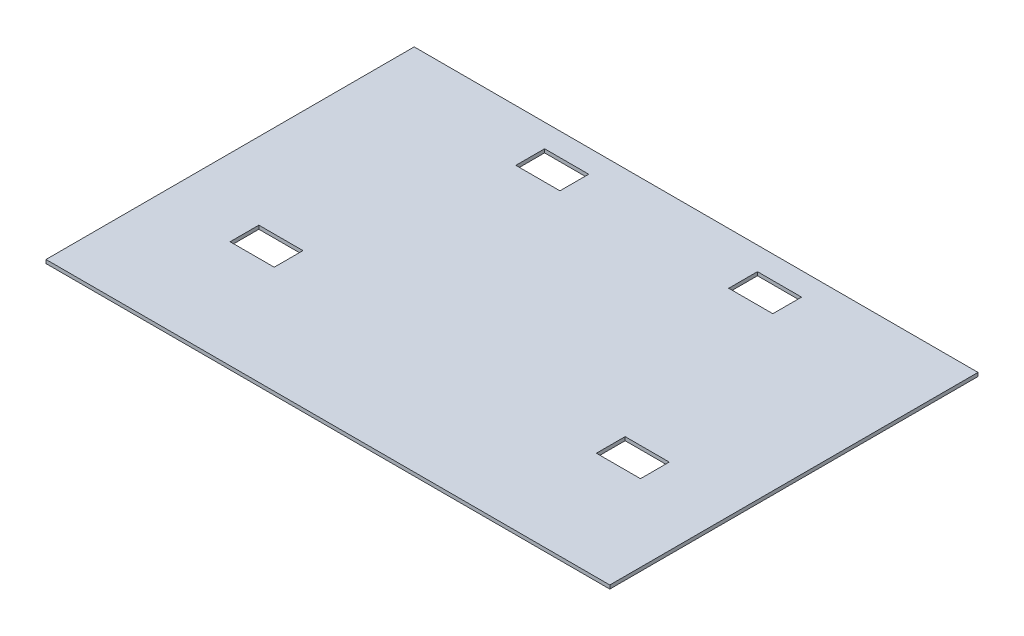
SolidWorks part; units mm, degrees
material "Pine"
ref_plane "Front Plane" through (0, 0, 0) normal (0, 0, 1) x (1, 0, 0)
ref_plane "Top Plane" through (0, 0, 0) normal (0, 1, 0) x (1, 0, 0)
ref_plane "Right Plane" through (0, 0, 0) normal (1, 0, 0) x (0, 0, -1)
other "Configuration Table"
sketch "Sketch1" plane through (0, 0, 0) normal (0, 1, 0) x (1, 0, 0)
  line L1 (-933.45, -609.6) -> (933.45, -609.6)
  line L2 (-933.45, -609.6) -> (-933.45, 609.6)
  line L3 (-933.45, 609.6) -> (933.45, 609.6)
  line L4 (933.45, -609.6) -> (933.45, 609.6)
  line L5 (-933.45, -609.6) -> (933.45, 609.6) construction
  line L6 (-933.45, 609.6) -> (933.45, -609.6) construction
  point P0 (0, 0)
  dimension "D1" = 1866.9
  dimension "D2" = 1219.2
extrude "Boss-Extrude1" add sketch "Sketch1" along normal mid plane 11.9062
sketch "Sketch2" [suppressed] plane through (0, 6.35, 0) normal (0, 1, 0) x (1, 0, 0)
  line L0 (1219.2, 609.6) -> (-1219.2, 609.6) construction
  line L1 (-1219.2, -609.6) -> (406.4, -609.6)
  line L2 (-1219.2, -609.6) -> (-1219.2, 254)
  line L3 (-1219.2, 254) -> (406.4, 254)
  line L4 (406.4, -609.6) -> (406.4, 254)
  line L5 (1219.2, -609.6) -> (1219.2, 609.6) construction
  dimension "D1" = 355.6
  dimension "D2" = 812.8
extrude "Cut-Extrude1" [suppressed] cut sketch "Sketch2" against normal through all
sketch "Sketch3" [suppressed] plane through (0, -5.9531, 0) normal (0, -1, 0) x (1, 0, 0)
  line L0 (58.7375, -28.575) -> (-58.7375, -28.575) construction
  line L1 (385.7625, -304.8) -> (-385.7625, -304.8) construction
  line L2 (-14.2875, 19.05) -> (131.7625, 19.05)
  line L3 (-14.2875, 19.05) -> (-14.2875, -76.2)
  line L4 (-14.2875, -76.2) -> (131.7625, -76.2)
  line L5 (131.7625, 19.05) -> (131.7625, -76.2)
  line L6 (-14.2875, 19.05) -> (131.7625, -76.2) construction
  line L7 (-14.2875, -76.2) -> (131.7625, 19.05) construction
  line L8 (-131.7625, 19.05) -> (14.2875, 19.05)
  line L9 (-131.7625, 19.05) -> (-131.7625, -76.2)
  line L10 (-131.7625, -76.2) -> (14.2875, -76.2)
  line L11 (14.2875, 19.05) -> (14.2875, -76.2)
  line L12 (-131.7625, 19.05) -> (14.2875, -76.2) construction
  line L13 (-131.7625, -76.2) -> (14.2875, 19.05) construction
  line L14 (385.7625, 304.8) -> (385.7625, -304.8) construction
  point P4 (0, -28.575)
  dimension "D1" = 146.05
  dimension "D2" = 95.25
  dimension "D3" = 254
  dimension "D4" = 228.6
extrude "Cut-Extrude2" [suppressed] cut sketch "Sketch3" against normal through all
sketch "Sketch12" [suppressed] plane through (0, 6.35, 0) normal (0, 1, 0) x (1, 0, 0)
  line L0 (-127, -317.5) -> (685.8, -317.5) construction
  line L1 (542.925, -220.6625) -> (446.0875, -220.6625)
  line L2 (542.925, -220.6625) -> (542.925, -317.5)
  line L3 (542.925, -317.5) -> (446.0875, -317.5)
  line L4 (446.0875, -220.6625) -> (446.0875, -317.5)
  line L5 (685.8, -317.5) -> (685.8, 317.5) construction
  line L6 (-127, -317.5) -> (-127, -38.1) construction
  line L7 (38.1, -220.6625) -> (134.9375, -220.6625)
  line L8 (38.1, -220.6625) -> (38.1, -317.5)
  line L9 (38.1, -317.5) -> (134.9375, -317.5)
  line L10 (134.9375, -220.6625) -> (134.9375, -317.5)
  dimension "D1" = 96.8375
  dimension "D2" = 142.875
  dimension "D3" = 165.1
extrude "Cut-Extrude10" [suppressed] cut sketch "Sketch12" against normal through all
sketch "Sketch11" [suppressed] plane through (0, -5.9531, 0) normal (0, -1, 0) x (1, 0, 0)
  line L0 (385.7625, 304.8) -> (385.7625, -304.8) construction
  line L1 (334.9625, 65.0875) -> (385.7625, 65.0875)
  line L2 (334.9625, 65.0875) -> (334.9625, 161.925)
  line L3 (334.9625, 161.925) -> (385.7625, 161.925)
  line L4 (385.7625, 65.0875) -> (385.7625, 161.925)
  line L5 (385.7625, -304.8) -> (-385.7625, -304.8) construction
  line L6 (-385.7625, 304.8) -> (385.7625, 304.8) construction
  line L7 (334.9625, -47.625) -> (385.7625, -47.625)
  line L8 (334.9625, -47.625) -> (334.9625, -144.4625)
  line L9 (334.9625, -144.4625) -> (385.7625, -144.4625)
  line L10 (385.7625, -47.625) -> (385.7625, -144.4625)
  dimension "D1" = 50.8
  dimension "D2" = 96.8375
  dimension "D3" = 142.875
  dimension "D4" = 160.3375
extrude "Cut-Extrude9" [suppressed] cut sketch "Sketch11" against normal through all
sketch "Sketch4" plane through (0, -5.9531, 0) normal (0, -1, 0) x (1, 0, 0)
  line L0 (0, 206.375) -> (0, -485.775) construction
  line L1 (606.425, 206.375) -> (-606.425, 206.375) construction
  line L2 (352.425, -485.775) -> (-352.425, -485.775) construction
  line L3 (933.45, 609.6) -> (933.45, -609.6) construction
  line L4 (425.45, -533.4) -> (279.4, -533.4)
  line L5 (425.45, -533.4) -> (425.45, -438.15)
  line L6 (425.45, -438.15) -> (279.4, -438.15)
  line L7 (279.4, -533.4) -> (279.4, -438.15)
  line L8 (425.45, -533.4) -> (279.4, -438.15) construction
  line L9 (425.45, -438.15) -> (279.4, -533.4) construction
  line L10 (-279.4, -533.4) -> (-425.45, -533.4)
  line L11 (-279.4, -533.4) -> (-279.4, -438.15)
  line L12 (-279.4, -438.15) -> (-425.45, -438.15)
  line L13 (-425.45, -533.4) -> (-425.45, -438.15)
  line L14 (-279.4, -533.4) -> (-425.45, -438.15) construction
  line L15 (-279.4, -438.15) -> (-425.45, -533.4) construction
  line L16 (-533.4, 158.75) -> (-679.45, 158.75)
  line L17 (-533.4, 158.75) -> (-533.4, 254)
  line L18 (-533.4, 254) -> (-679.45, 254)
  line L19 (-679.45, 158.75) -> (-679.45, 254)
  line L20 (-533.4, 158.75) -> (-679.45, 254) construction
  line L21 (-533.4, 254) -> (-679.45, 158.75) construction
  line L22 (679.45, 158.75) -> (533.4, 158.75)
  line L23 (679.45, 158.75) -> (679.45, 254)
  line L24 (679.45, 254) -> (533.4, 254)
  line L25 (533.4, 158.75) -> (533.4, 254)
  line L26 (679.45, 158.75) -> (533.4, 254) construction
  line L27 (679.45, 254) -> (533.4, 158.75) construction
  line L29 (-933.45, 609.6) -> (933.45, 609.6) construction
  line L30 (933.45, -609.6) -> (-933.45, -609.6) construction
  point P8 (0, 206.375)
  point P11 (0, -485.775)
  dimension "D1" = 146.05
  dimension "D2" = 95.25
  dimension "D3" = 254
  dimension "D4" = 76.2
  dimension "D5" = 355.6
  dimension "D6" = 508
extrude "Cut-Extrude3" cut sketch "Sketch4" against normal through all
sketch "Sketch5" [suppressed] plane through (0, 6.35, 0) normal (0, 1, 0) x (1, 0, 0)
  line L0 (-127, -38.1) -> (-685.8, -38.1) construction
  line L1 (685.8, 317.5) -> (-685.8, 317.5) construction
  line L3 (685.8, -317.5) -> (685.8, 317.5) construction
  line L4 (282.575, 317.5) -> (282.575, -317.5) construction
  line L5 (-358.775, 66.675) -> (-454.025, 66.675)
  line L6 (-358.775, 66.675) -> (-358.775, 212.725)
  line L7 (-358.775, 212.725) -> (-454.025, 212.725)
  line L8 (-454.025, 66.675) -> (-454.025, 212.725)
  line L9 (-358.775, 66.675) -> (-454.025, 212.725) construction
  line L10 (-358.775, 212.725) -> (-454.025, 66.675) construction
  line L11 (-127, -317.5) -> (38.1, -317.5) construction
  line L12 (-685.8, 317.5) -> (-685.8, -38.1) construction
  line L13 (234.95, 66.675) -> (330.2, 66.675)
  line L14 (234.95, 66.675) -> (234.95, 212.725)
  line L15 (234.95, 212.725) -> (330.2, 212.725)
  line L16 (330.2, 66.675) -> (330.2, 212.725)
  line L17 (234.95, 66.675) -> (330.2, 212.725) construction
  line L18 (234.95, 212.725) -> (330.2, 66.675) construction
  line L19 (234.95, -212.725) -> (330.2, -212.725)
  line L20 (234.95, -212.725) -> (234.95, -66.675)
  line L21 (234.95, -66.675) -> (330.2, -66.675)
  line L22 (330.2, -212.725) -> (330.2, -66.675)
  line L23 (234.95, -212.725) -> (330.2, -66.675) construction
  line L24 (234.95, -66.675) -> (330.2, -212.725) construction
  point P8 (-406.4, 139.7)
  point P17 (282.575, 139.7)
  point P23 (282.575, -139.7)
  point P31 (-406.4, 139.7)
  dimension "D1" = 355.6
  dimension "D2" = 95.25
  dimension "D3" = 146.05
  dimension "D4" = 104.775
  dimension "D5" = 104.775
  dimension "D6" = 231.775
extrude "Cut-Extrude4" [suppressed] cut sketch "Sketch5" against normal through all
sketch "Sketch6" [suppressed] plane through (0, 5.9531, 0) normal (0, 1, 0) x (1, 0, 0)
  line L0 (385.7625, -304.8) -> (385.7625, 304.8) construction
  line L1 (157.1625, -73.025) -> (61.9125, -73.025)
  line L2 (157.1625, -73.025) -> (157.1625, 73.025)
  line L3 (157.1625, 73.025) -> (61.9125, 73.025)
  line L4 (61.9125, -73.025) -> (61.9125, 73.025)
  line L5 (157.1625, -73.025) -> (61.9125, 73.025) construction
  line L6 (157.1625, 73.025) -> (61.9125, -73.025) construction
  point P0 (109.5375, 0)
  dimension "D1" = 95.25
  dimension "D2" = 146.05
  dimension "D3" = 228.6
extrude "Cut-Extrude5" [suppressed] cut sketch "Sketch6" against normal through all
sketch "Sketch7" [suppressed] plane through (0, -6.35, 0) normal (0, -1, 0) x (1, 0, 0)
  line L0 (-933.45, -275.4312) -> (-933.45, 275.4313) construction
  line L1 (47.625, -275.4312) -> (-49.2125, -275.4312)
  line L2 (47.625, -275.4312) -> (47.625, -178.5937)
  line L3 (47.625, -178.5937) -> (-49.2125, -178.5937)
  line L4 (-49.2125, -275.4312) -> (-49.2125, -178.5937)
  line L6 (-557.2125, -275.4313) -> (-654.05, -275.4312)
  line L7 (-557.2125, -275.4313) -> (-557.2125, -178.5938)
  line L8 (-557.2125, -178.5938) -> (-654.05, -178.5938)
  line L9 (-654.05, -275.4312) -> (-654.05, -178.5938)
  line L10 (-654.05, -275.4312) -> (654.05, -275.4313) construction
  line L11 (654.05, -275.4313) -> (557.2125, -275.4313)
  line L12 (654.05, -275.4313) -> (654.05, -178.5937)
  line L13 (654.05, -178.5937) -> (557.2125, -178.5938)
  line L14 (557.2125, -275.4313) -> (557.2125, -178.5938)
  line L17 (933.45, -275.4312) -> (-933.45, -275.4312) construction
  point P12 (0, -275.4313)
  dimension "D1" = 96.8375
  dimension "D2" = 279.4
  dimension "D3" = 884.2375
extrude "Cut-Extrude6" [suppressed] cut sketch "Sketch7" against normal through all
sketch "Sketch8" [suppressed] plane through (0, 5.9531, 0) normal (0, 1, 0) x (1, 0, 0)
  line L0 (-385.7625, 304.8) -> (-385.7625, -304.8) construction
  line L1 (-385.7625, 79.375) -> (-288.925, 79.375)
  line L2 (-385.7625, 79.375) -> (-385.7625, 176.2125)
  line L3 (-385.7625, 176.2125) -> (-288.925, 176.2125)
  line L4 (-288.925, 79.375) -> (-288.925, 176.2125)
  line L6 (385.7625, 304.8) -> (-385.7625, 304.8) construction
  dimension "D1" = 96.8375
  dimension "D2" = 128.5875
extrude "Cut-Extrude7" [suppressed] cut sketch "Sketch8" against normal through all
sketch "Sketch10" [suppressed] plane through (0, 6.35, 0) normal (0, 1, 0) x (1, 0, 0)
  line L0 (-127, -317.5) -> (-127, -38.1) construction
  line L1 (-76.2, -271.4625) -> (-127, -271.4625)
  line L2 (-76.2, -271.4625) -> (-76.2, -174.625)
  line L3 (-76.2, -174.625) -> (-127, -174.625)
  line L4 (-127, -271.4625) -> (-127, -174.625)
  line L6 (-127, -317.5) -> (38.1, -317.5) construction
  dimension "D1" = 50.8
  dimension "D2" = 96.8375
  dimension "D3" = 46.0375
extrude "Cut-Extrude8" [suppressed] cut sketch "Sketch10" against normal through all
sketch "Sketch13" [suppressed] plane through (0, -5.9531, 0) normal (0, -1, 0) x (1, 0, 0)
  line L0 (385.7625, -304.8) -> (-385.7625, -304.8) construction
  line L1 (-498.475, -254) -> (-595.3125, -254)
  line L2 (-498.475, -254) -> (-498.475, -304.8)
  line L3 (-498.475, -304.8) -> (-595.3125, -304.8)
  line L4 (-595.3125, -254) -> (-595.3125, -304.8)
  line L5 (107.1563, -254) -> (10.3188, -254)
  line L6 (107.1563, -254) -> (107.1563, -304.8)
  line L7 (107.1563, -304.8) -> (10.3188, -304.8)
  line L8 (10.3188, -254) -> (10.3188, -304.8)
  line L9 (-10.3188, -254) -> (-107.1563, -254)
  line L10 (-10.3188, -254) -> (-10.3188, -304.8)
  line L11 (-10.3188, -304.8) -> (-107.1563, -304.8)
  line L12 (-107.1563, -254) -> (-107.1563, -304.8)
  line L13 (10.3188, -254) -> (-10.3188, -254) construction
  line L14 (385.7625, 304.8) -> (385.7625, -304.8) construction
  line L15 (385.7625, 304.8) -> (385.7625, -304.8) construction
  point P14 (0, -254)
  dimension "D1" = 96.8375
  dimension "D2" = 50.8
  dimension "D3" = 278.6062
  dimension "D4" = 884.2375
extrude "Cut-Extrude11" [suppressed] cut sketch "Sketch13" against normal through all
